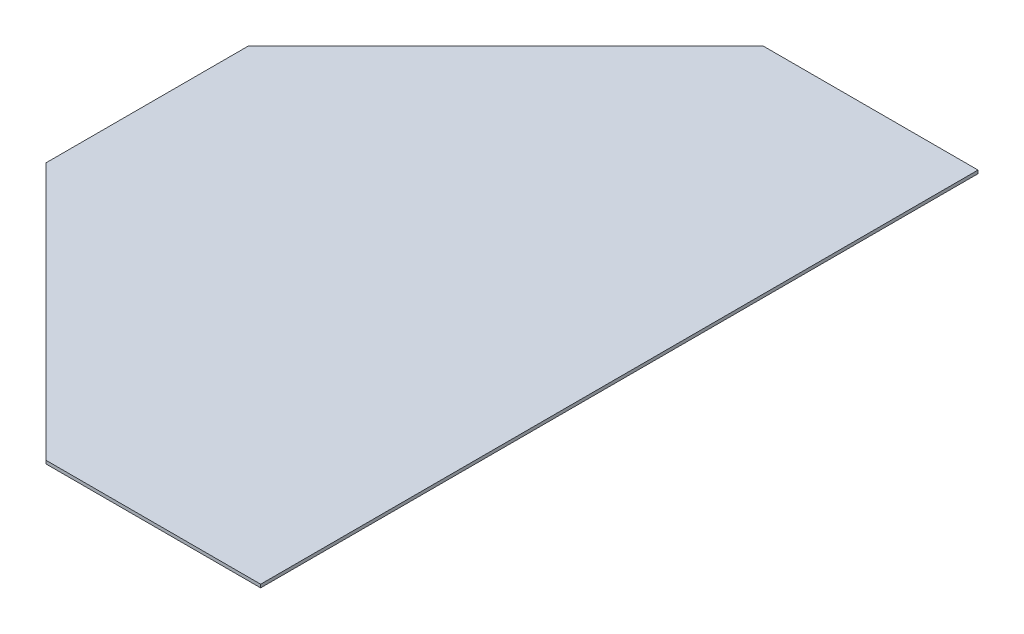
SolidWorks part; units mm, degrees
material "PVC Rigid"
ref_plane "Front Plane" through (0, 0, 0) normal (0, 0, 1) x (1, 0, 0)
ref_plane "Top Plane" through (0, 0, 0) normal (0, 1, 0) x (1, 0, 0)
ref_plane "Right Plane" through (0, 0, 0) normal (1, 0, 0) x (0, 0, -1)
sketch "Sketch1" plane through (0, 0, 0) normal (0, 1, 0) x (1, 0, 0)
  line L1 (0, 0) -> (440, 0)
  line L2 (0, 0) -> (0, 668.38)
  line L3 (0, 668.38) -> (440, 668.38)
  line L4 (440, 0) -> (440, 668.38)
  dimension "D1" = 440
  dimension "D2" = 668.38
extrude "Boss-Extrude1" add sketch "Sketch1" along normal blind 3
sketch "Sketch2" plane through (0, 0, 0) normal (0, -1, 0) x (1, 0, 0)
  line L0 (240, 0) -> (0, -240)
  line L2 (0, -668.38) -> (0, 0) construction
  line L3 (0, -240) -> (0, 0)
  line L4 (0, 0) -> (240, 0)
  line L6 (0, 0) -> (440, 0) construction
  line L7 (0, -428.38) -> (240, -668.38)
  line L8 (440, -668.38) -> (0, -668.38) construction
  line L9 (240, -668.38) -> (0, -668.38)
  line L10 (0, -668.38) -> (0, -428.38)
  dimension "D1" = 240
  dimension "D2" = 240
  dimension "D3" = 240
  dimension "D4" = 240
extrude "Cut-Extrude1" cut sketch "Sketch2" against normal through all
